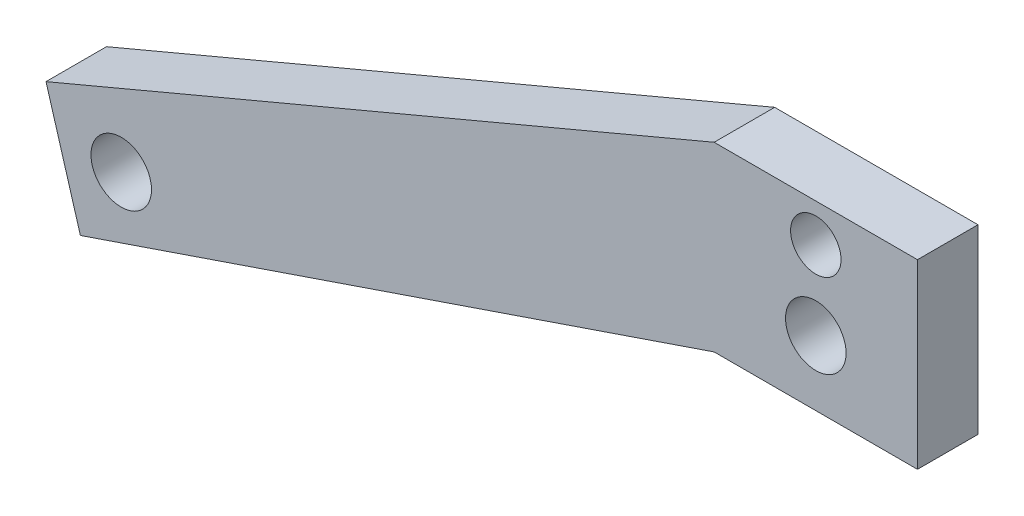
SolidWorks part; units mm, degrees
ref_plane "Front Plane" through (0, 0, 0) normal (0, 0, 1) x (1, 0, 0)
ref_plane "Top Plane" through (0, 0, 0) normal (0, 1, 0) x (1, 0, 0)
ref_plane "Right Plane" through (0, 0, 0) normal (1, 0, 0) x (0, 0, -1)
sketch "Sketch1" plane through (0, 0, 0) normal (0, 0, 1) x (1, 0, 0)
  line L0 (-16, 45) -> (-121.1436, 0.6973)
  line L2 (-276.7879, -13.7826) -> (-251.7788, -35.3348) construction
  line L3 (0, 26.6476) -> (-109.3056, -5.7302) construction
  line L4 (-16, 45) -> (-16, 15)
  line L5 (-16, 15) -> (16, 15)
  line L6 (16, 15) -> (16, 45)
  line L7 (16, 45) -> (-16, 45)
  line L8 (-16, 45) -> (-16, 16.425) construction
  line L9 (-16, 15) -> (16, 15) construction
  line L10 (16, 16.425) -> (16, 45)
  line L11 (16, 45) -> (-16, 45)
  line L12 (16, 16.425) -> (-16, 16.425)
  line L13 (-16, 16.425) -> (-115.7331, -17.5682)
  line L14 (-115.7331, -17.5682) -> (-121.1436, 0.6973)
  line L15 (-251.7788, -35.3348) -> (-242.2031, -37.4927) construction
  line L17 (-28.3991, 26.6361) -> (-28.037, 26.7) construction
  line L18 (-2117.156, -341.6) -> (-28.037, 26.7) construction
  line L19 (-242.2031, -37.4927) -> (-208.8903, -37.4927) construction
  line L20 (-208.8903, -37.4927) -> (-16, 45) construction
  line L21 (-292.5067, -43.5335) -> (-248.9466, -55.1606) construction
  line L22 (-248.9466, -55.1606) -> (-208.8903, -56.2396) construction
  line L23 (-208.8903, -56.2396) -> (-14.9476, 16.425) construction
  line L24 (-288.0555, -26.8574) -> (0, 26.6476) construction
  line L47 (-109.3056, -5.7302) -> (-118.4384, -8.4355) construction
  circle A0 centre (0, 39) radius 3.9688 construction
  circle A1 centre (0, 39) radius 3.9688
  circle A2 centre (0, 26.6476) radius 4.7625
  circle A3 centre (-109.3056, -5.7302) radius 4.7625
  circle A4 centre (-288.0555, -26.8574) radius 17.26 construction
  point P21 (-118.4384, -8.4355)
  dimension "D2" = 9.525
  dimension "D4" = 109.3056
  dimension "D7" = 292.9825
  dimension "D3" = 9.525
  dimension "D5" = 19.05
  dimension "D6" = 28.575
  dimension "D8" = 16.5
  dimension "D9" = 32
  dimension "D1" = 0
extrude "Boss-Extrude1" add sketch "Sketch1" along normal blind 9.525
